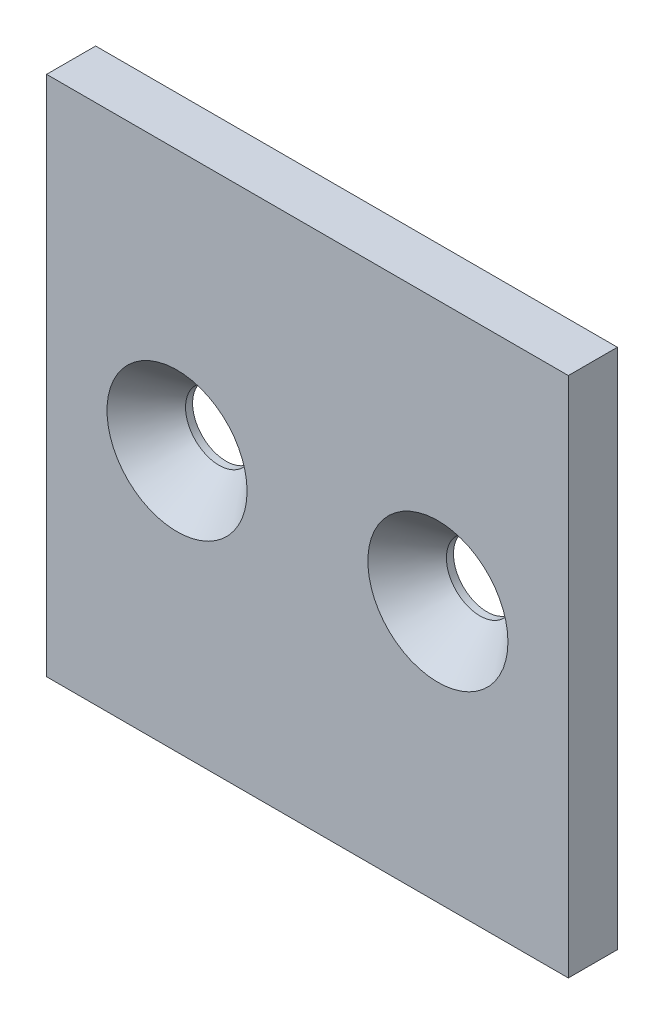
SolidWorks part; units mm, degrees
ref_plane "Front Plane" through (0, 0, 0) normal (0, 0, 1) x (1, 0, 0)
ref_plane "Top Plane" through (0, 0, 0) normal (0, 1, 0) x (1, 0, 0)
ref_plane "Right Plane" through (0, 0, 0) normal (1, 0, 0) x (0, 0, -1)
sketch "Sketch1" plane through (0, 0, 0) normal (0, 0, 1) x (1, 0, 0)
  line L0 (0, 0) -> (0, 50.8)
  line L1 (12.7, 25.4) -> (38.1, 25.4) construction
  line L4 (50.8, 50.8) -> (0, 50.8)
  line L5 (50.8, 0) -> (0, 0)
  line L7 (50.8, 50.8) -> (50.8, 0)
  circle A0 centre (12.7, 25.4) radius 3.2639
  circle A1 centre (38.1, 25.4) radius 3.2639
  dimension "D1" = 25.4
  dimension "E" = 6.5278
  dimension "D2" = 12.7
  dimension "C" = 50.8
  dimension "D3" = 25.4
  dimension "B" = 50.8
extrude "Boss-Extrude1" add sketch "Sketch1" along normal mid plane 4.7752
sketch "Sketch2" plane through (0, 0, 2.3876) normal (0, 0, 1) x (1, 0, 0)
  circle A0 centre (12.7, 25.4) radius 3.2639 construction
  circle A1 centre (12.7, 25.4) radius 3.2639
  circle A2 centre (38.1, 25.4) radius 3.2639 construction
  circle A3 centre (38.1, 25.4) radius 3.2639
extrude "Cut-Extrude1" cut sketch "Sketch2" along normal through all draft 41 from offset 4.0894 offset against normal yes
ref_plane "CenterPlane1" through (25.4, 0, 0) normal (-1, 0, 0) x (0, 0, 1)
